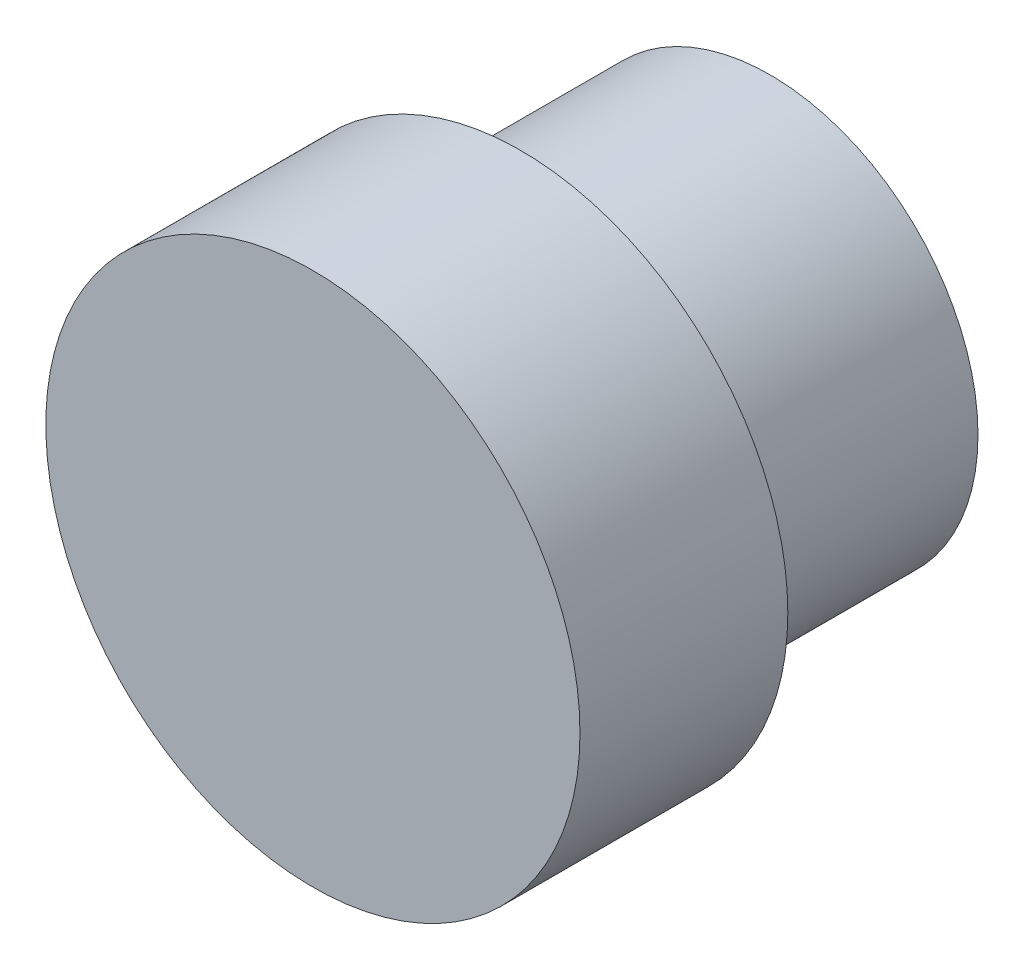
SolidWorks part; units mm, degrees
ref_plane "Front Plane" through (0, 0, 0) normal (0, 0, 1) x (1, 0, 0)
ref_plane "Top Plane" through (0, 0, 0) normal (0, 1, 0) x (1, 0, 0)
ref_plane "Right Plane" through (0, 0, 0) normal (1, 0, 0) x (0, 0, -1)
sketch "Sketch2" plane through (0, 0, 0) normal (0, 0, 1) x (1, 0, 0)
  circle A0 centre (15, 15) radius 5
extrude "Boss-Extrude1" add sketch "Sketch2" along normal blind 6
sketch "Sketch3" plane through (0, 0, 6) normal (0, 0, 1) x (1, 0, 0)
  circle A0 centre (15, 15) radius 6.425
extrude "Boss-Extrude2" add sketch "Sketch3" along normal blind 5
